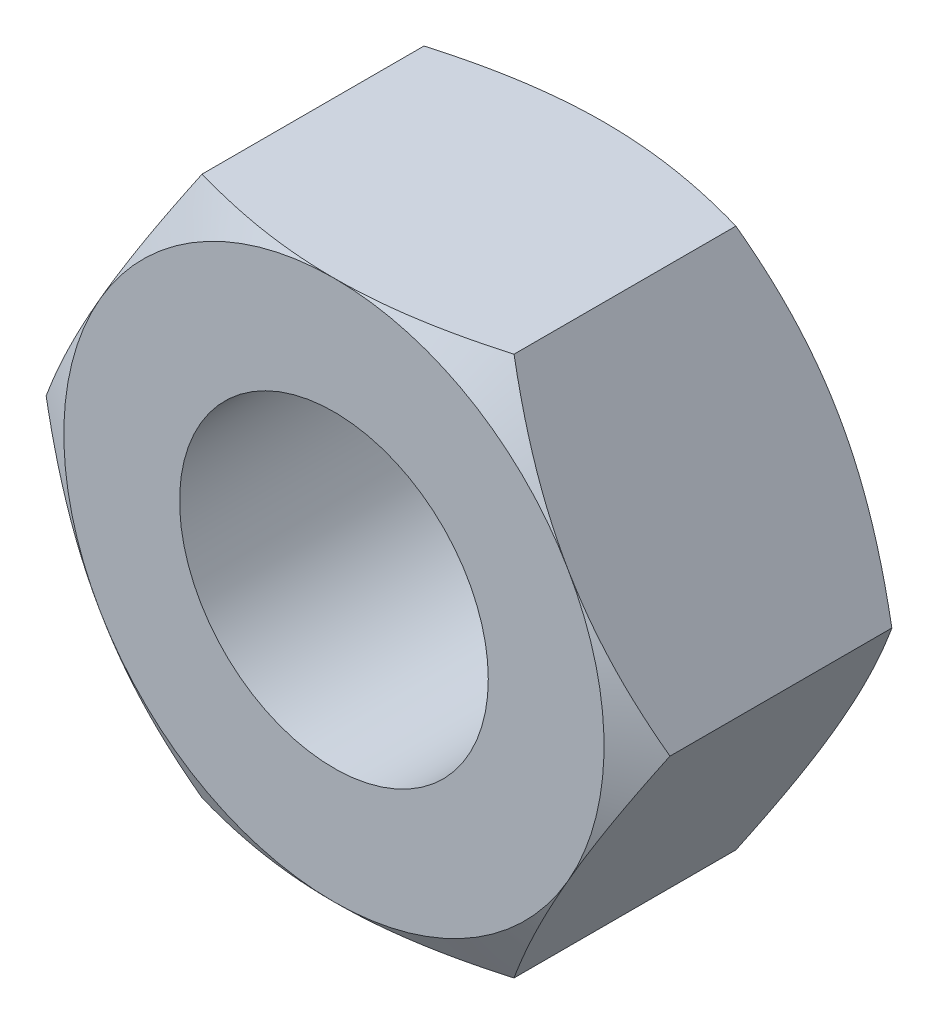
SolidWorks part; units mm, degrees
ref_plane "Top" through (0, 0, 0) normal (0, 0, 1) x (1, 0, 0)
ref_plane "Plane2" through (0, 0, 0) normal (0, 1, 0) x (1, 0, 0)
ref_plane "Plane3" through (0, 0, 0) normal (1, 0, 0) x (0, 0, -1)
extrude "Base-Extrude" add sketch "Sketch2" against normal blind 5.5562
sketch "Sketch2" plane through (0, 0, 0) normal (0, 0, 1) x (1, 0, 0)
  line L1 (3.2079, -5.5563) -> (6.4158, 0)
  line L2 (6.4158, 0) -> (3.2079, 5.5563)
  line L3 (3.2079, 5.5563) -> (-3.2079, 5.5563)
  line L4 (-3.2079, 5.5563) -> (-6.4158, 0)
  line L5 (-6.4158, 0) -> (-3.2079, -5.5563)
  line L6 (-3.2079, -5.5563) -> (3.2079, -5.5563)
  circle A0 centre (0, 0) radius 5.5562 construction
  dimension "Flats" = 11.1125
extrude "I.D." cut sketch "Sketch4" against normal through all
sketch "Sketch4" plane through (0, 0, 0) normal (0, 0, 1) x (1, 0, 0)
  circle A0 centre (0, 0) radius 3.175
  dimension "I.D." = 6.35
sketch "Sketch5" plane through (0, 0, -5.5562) normal (0, 0, -1) x (-1, 0, 0)
  line L0 (3.2079, -5.5563) -> (-3.2079, -5.5563) construction
  circle A0 centre (0, 0) radius 5.5563
extrude "Cut-Extrude3" cut sketch "Sketch5" against normal blind 25.4 draft 60 flip side to cut
sketch "Sketch6" plane through (0, 0, 0) normal (0, 0, 1) x (1, 0, 0)
  circle A0 centre (0, 0) radius 5.5562 construction
  circle A1 centre (0, 0) radius 5.5562
extrude "Cut-Extrude4" cut sketch "Sketch6" against normal blind 10 draft 60 flip side to cut
